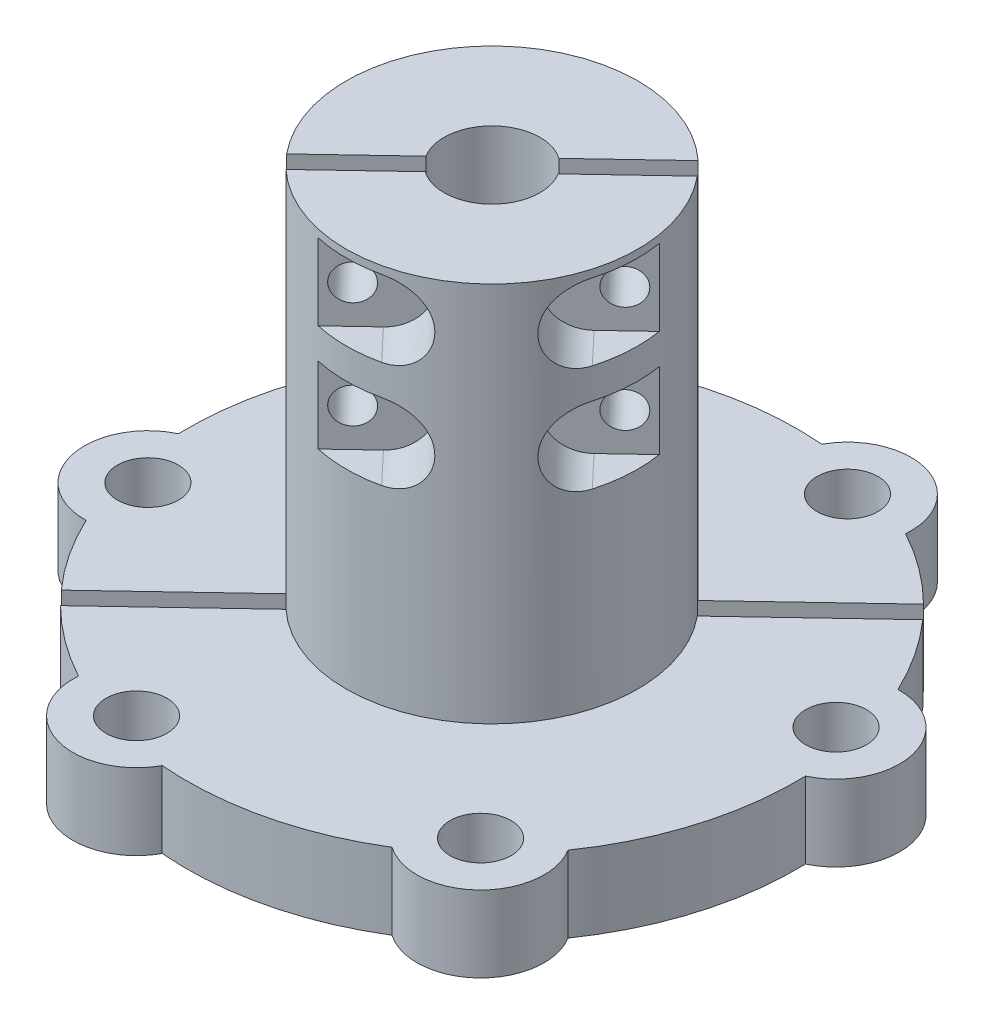
SolidWorks part; units mm, degrees
ref_plane "Front" through (0, 0, 0) normal (0, 0, 1) x (1, 0, 0)
ref_plane "Top" through (0, 0, 0) normal (0, 1, 0) x (1, 0, 0)
ref_plane "Right" through (0, 0, 0) normal (1, 0, 0) x (0, 0, -1)
sketch "Sketch1" plane through (0, 0, 0) normal (0, 1, 0) x (1, 0, 0)
  circle A0 centre (0, 0) radius 29.3688
  circle A1 centre (0, 0) radius 4
  dimension "D1" = 58.7375
  dimension "D2" = 8
extrude "Boss-Extrude1" add sketch "Sketch1" along normal blind 6.35
sketch "Sketch3" plane through (0, 6.35, 0) normal (0, 1, 0) x (1, 0, 0)
  circle A0 centre (0, 0) radius 4 construction
  circle A1 centre (0, 0) radius 4
  circle A2 centre (0, 0) radius 12.1539
  dimension "D1" = 24.3078
extrude "Boss-Extrude2" add sketch "Sketch3" along normal blind 31.75
sketch "Sketch4" plane through (0, 6.35, 0) normal (0, 1, 0) x (1, 0, 0)
  circle A0 centre (0, 0) radius 51.9218
  arc A1 (25.4208, 0.7099) -> (23.0191, 10.8093) centre (23.1665, 5.5091) ccw
  arc A2 (23.0191, 10.8093) -> (12.0949, 22.3703) centre (0, 0) ccw
  arc A3 (12.0949, 22.3703) -> (2.1481, 25.3398) centre (6.8115, 22.8166) ccw
  arc A4 (2.1481, 25.3398) -> (-13.3267, 21.6591) centre (0, 0) ccw
  arc A5 (-13.3267, 21.6591) -> (-20.8715, 14.5293) centre (-16.3548, 17.3065) ccw
  arc A6 (-20.8715, 14.5293) -> (-25.4207, -0.7121) centre (0, 0) ccw
  arc A7 (-25.4207, -0.7121) -> (-23.0182, -10.8112) centre (-23.166, -5.5111) ccw
  arc A8 (-23.0182, -10.8112) -> (-12.0943, -22.3707) centre (0, 0) ccw
  arc A9 (-12.0943, -22.3707) -> (-2.1466, -25.3399) centre (-6.811, -22.8186) ccw
  arc A10 (-2.1466, -25.3399) -> (13.3255, -21.6599) centre (0, 0) ccw
  arc A11 (13.3255, -21.6599) -> (20.8711, -14.5299) centre (16.3552, -17.3085) ccw
  arc A12 (25.6787, 0.5533) -> (23.1789, 11.0653) centre (23.1665, 5.5091) ccw
  arc A13 (21.1727, -14.5402) -> (25.6787, 0.5533) centre (0, 0) ccw
  arc A14 (13.3188, -21.9616) -> (21.1727, -14.5402) centre (16.3552, -17.3085) ccw
  arc A15 (-2.0047, -25.6063) -> (13.3188, -21.9616) centre (0, 0) ccw
  arc A16 (-12.359, -22.5157) -> (-2.0047, -25.6063) centre (-6.811, -22.8186) ccw
  arc A17 (-23.178, -11.0673) -> (-12.359, -22.5157) centre (0, 0) ccw
  arc A18 (-25.6787, -0.5554) -> (-23.178, -11.0673) centre (-23.166, -5.5111) ccw
  arc A19 (-21.1731, 14.5397) -> (-25.6787, -0.5554) centre (0, 0) ccw
  arc A20 (-13.3201, 21.9608) -> (-21.1731, 14.5397) centre (-16.3548, 17.3065) ccw
  arc A21 (2.0063, 25.6062) -> (-13.3201, 21.9608) centre (0, 0) ccw
  arc A22 (12.3596, 22.5154) -> (2.0063, 25.6062) centre (6.8115, 22.8166) ccw
  arc A23 (23.1789, 11.0653) -> (12.3596, 22.5154) centre (0, 0) ccw
  arc A24 (25.6787, 0.5533) -> (23.1789, 11.0653) centre (23.1665, 5.5091) ccw construction
  arc A25 (21.1727, -14.5402) -> (25.6787, 0.5533) centre (0, 0) ccw construction
  arc A26 (13.3188, -21.9616) -> (21.1727, -14.5402) centre (16.3552, -17.3085) ccw construction
  arc A27 (-2.0047, -25.6063) -> (13.3188, -21.9616) centre (0, 0) ccw construction
  arc A28 (-12.359, -22.5157) -> (-2.0047, -25.6063) centre (-6.811, -22.8186) ccw construction
  arc A29 (-23.178, -11.0673) -> (-12.359, -22.5157) centre (0, 0) ccw construction
  arc A30 (-25.6787, -0.5554) -> (-23.178, -11.0673) centre (-23.166, -5.5111) ccw construction
  arc A31 (-21.1731, 14.5397) -> (-25.6787, -0.5554) centre (0, 0) ccw construction
  arc A32 (-13.3201, 21.9608) -> (-21.1731, 14.5397) centre (-16.3548, 17.3065) ccw construction
  arc A33 (2.0063, 25.6062) -> (-13.3201, 21.9608) centre (0, 0) ccw construction
  arc A34 (12.3596, 22.5154) -> (2.0063, 25.6062) centre (6.8115, 22.8166) ccw construction
  arc A35 (23.1789, 11.0653) -> (12.3596, 22.5154) centre (0, 0) ccw construction
  arc A36 (20.8711, -14.5299) -> (25.4208, 0.7099) centre (0, 0) ccw
  dimension "D2" = 0.254
  dimension "D1" = 0
extrude "Cut-Extrude1" cut sketch "Sketch4" against normal through all
sketch "Sketch5" plane through (0, 6.35, 0) normal (0, 1, 0) x (1, 0, 0)
  circle A0 centre (-23.166, -5.5111) radius 2.54 construction
  circle A1 centre (-6.811, -22.8186) radius 2.54 construction
  circle A2 centre (16.3552, -17.3085) radius 2.54 construction
  circle A3 centre (23.1665, 5.5091) radius 2.54 construction
  circle A4 centre (6.8115, 22.8166) radius 2.54 construction
  circle A5 centre (-16.3548, 17.3065) radius 2.54 construction
  circle A6 centre (-23.166, -5.5111) radius 2.54
  circle A7 centre (-6.811, -22.8186) radius 2.54
  circle A8 centre (16.3552, -17.3085) radius 2.54
  circle A9 centre (23.1665, 5.5091) radius 2.54
  circle A10 centre (6.8115, 22.8166) radius 2.54
  circle A11 centre (-16.3548, 17.3065) radius 2.54
extrude "Cut-Extrude2" cut sketch "Sketch5" against normal through all
sketch "Sketch6" plane through (0, 0, 0) normal (0, -1, 0) x (1, 0, 0)
  circle A0 centre (0, 0) radius 9.525
  dimension "D1" = 19.05
extrude "Cut-Extrude3" cut sketch "Sketch6" against normal blind 12.7
sketch "Outline" plane through (0, 0, 0) normal (0, -1, 0) x (1, 0, 0)
  circle A0 centre (0, 0) radius 9.525 construction
  circle A1 centre (0, 0) radius 9.525
  arc A12 (25.4208, -0.7099) -> (20.8711, 14.5299) centre (0, 0) ccw
  arc A13 (20.8711, 14.5299) -> (13.3255, 21.6599) centre (16.3552, 17.3085) ccw
  arc A14 (13.3255, 21.6599) -> (-2.1466, 25.3399) centre (0, 0) ccw
  arc A15 (-2.1466, 25.3399) -> (-12.0943, 22.3707) centre (-6.811, 22.8186) ccw
  arc A16 (-12.0943, 22.3707) -> (-23.0182, 10.8112) centre (0, 0) ccw
  arc A17 (-23.0182, 10.8112) -> (-25.4207, 0.7121) centre (-23.166, 5.5111) ccw
  arc A18 (-25.4207, 0.7121) -> (-20.8715, -14.5293) centre (0, 0) ccw
  arc A19 (-20.8715, -14.5293) -> (-13.3267, -21.6591) centre (-16.3548, -17.3065) ccw
  arc A20 (-13.3267, -21.6591) -> (2.1481, -25.3398) centre (0, 0) ccw
  arc A21 (2.1481, -25.3398) -> (12.0949, -22.3703) centre (6.8115, -22.8166) ccw
  arc A22 (12.0949, -22.3703) -> (23.0191, -10.8093) centre (0, 0) ccw
  arc A23 (23.0191, -10.8093) -> (25.4208, -0.7099) centre (23.1665, -5.5091) ccw
  arc A24 (25.4208, -0.7099) -> (20.8711, 14.5299) centre (0, 0) ccw
  arc A25 (20.8711, 14.5299) -> (13.3255, 21.6599) centre (16.3552, 17.3085) ccw
  arc A26 (13.3255, 21.6599) -> (-2.1466, 25.3399) centre (0, 0) ccw
  arc A27 (-2.1466, 25.3399) -> (-12.0943, 22.3707) centre (-6.811, 22.8186) ccw
  arc A28 (-12.0943, 22.3707) -> (-23.0182, 10.8112) centre (0, 0) ccw
  arc A29 (-23.0182, 10.8112) -> (-25.4207, 0.7121) centre (-23.166, 5.5111) ccw
  arc A30 (-25.4207, 0.7121) -> (-20.8715, -14.5293) centre (0, 0) ccw
  arc A31 (-20.8715, -14.5293) -> (-13.3267, -21.6591) centre (-16.3548, -17.3065) ccw
  arc A32 (-13.3267, -21.6591) -> (2.1481, -25.3398) centre (0, 0) ccw
  arc A33 (2.1481, -25.3398) -> (12.0949, -22.3703) centre (6.8115, -22.8166) ccw
  arc A34 (12.0949, -22.3703) -> (23.0191, -10.8093) centre (0, 0) ccw
  arc A35 (23.0191, -10.8093) -> (25.4208, -0.7099) centre (23.1665, -5.5091) ccw
  dimension "D1" = 0
sketch "Sketch7" plane through (0, 0, 0) normal (0, -1, 0) x (1, 0, 0)
  line L0 (-18.4831, 17.4669) -> (18.4841, -17.4659) construction
  line L1 (-23.8841, 21.4785) -> (22.7947, -22.6313)
  line L2 (-22.7937, 22.6323) -> (23.885, -21.4775)
  line L3 (-17.938, 18.0438) -> (19.0293, -16.889) construction
  line L4 (-19.0283, 16.89) -> (17.9389, -18.0428) construction
  arc A0 (-12.0943, 22.3707) -> (-23.0182, 10.8112) centre (0, 0) ccw construction
  arc A1 (12.0949, -22.3703) -> (23.0191, -10.8093) centre (0, 0) ccw construction
  arc A2 (-22.7937, 22.6323) -> (-23.8841, 21.4785) centre (0, 0) ccw
  arc A3 (22.7947, -22.6313) -> (23.885, -21.4775) centre (0, 0) ccw
  dimension "D1" = 0.7937
  dimension "D2" = 0.7937
extrude "Slot" cut sketch "Sketch7" against normal through all
ref_plane "Plane1" through (-25.6223, 0, -27.1146) normal (-0.6868, 0, -0.7268) x (-0.7268, 0, 0.6868)
sketch "Sketch8" plane through (-25.6223, 0, -27.1146) normal (-0.6868, 0, -0.7268) x (-0.7268, 0, 0.6868)
  line L0 (8.0241, 38.1) -> (8.0241, 34.29) construction
  line L1 (8.0241, 34.29) -> (8.0241, 25.4) construction
  line L2 (3.9203, 12.7) -> (-3.9203, 12.7) construction
  line L3 (0, 12.7) -> (0, 58.6753) construction
  line L8 (12.1279, 38.1) -> (3.9203, 38.1)
  line L9 (3.9203, 38.1) -> (3.9203, 12.7)
  line L10 (3.9203, 12.7) -> (9.4918, 12.7)
  line L11 (9.4918, 12.7) -> (9.4918, 0)
  line L12 (9.4918, 0) -> (25.4183, 0)
  line L13 (25.4183, 0) -> (25.4183, 6.35)
  line L14 (25.4183, 6.35) -> (12.1279, 6.35)
  line L15 (12.1279, 6.35) -> (12.1279, 38.1)
  line L16 (12.1279, 38.1) -> (3.9203, 38.1) construction
  line L17 (3.9203, 38.1) -> (3.9203, 12.7) construction
  line L18 (3.9203, 12.7) -> (9.4918, 12.7) construction
  line L19 (9.4918, 12.7) -> (9.4918, 0) construction
  line L20 (9.4918, 0) -> (25.4183, 0) construction
  line L21 (25.4183, 0) -> (25.4183, 6.35) construction
  line L22 (25.4183, 6.35) -> (12.1279, 6.35) construction
  line L23 (12.1279, 6.35) -> (12.1279, 38.1) construction
  line L24 (-12.1279, 6.35) -> (-25.4183, 6.35)
  line L25 (-25.4183, 6.35) -> (-25.4183, 0)
  line L26 (-25.4183, 0) -> (-9.4918, 0)
  line L27 (-9.4918, 0) -> (-9.4918, 12.7)
  line L28 (-9.4918, 12.7) -> (-3.9203, 12.7)
  line L29 (-3.9203, 12.7) -> (-3.9203, 38.1)
  line L30 (-3.9203, 38.1) -> (-12.1279, 38.1)
  line L31 (-12.1279, 38.1) -> (-12.1279, 6.35)
  line L32 (-12.1279, 6.35) -> (-25.4183, 6.35) construction
  line L33 (-25.4183, 6.35) -> (-25.4183, 0) construction
  line L34 (-25.4183, 0) -> (-9.4918, 0) construction
  line L35 (-9.4918, 0) -> (-9.4918, 12.7) construction
  line L36 (-9.4918, 12.7) -> (-3.9203, 12.7) construction
  line L37 (-3.9203, 12.7) -> (-3.9203, 38.1) construction
  line L38 (-3.9203, 38.1) -> (-12.1279, 38.1) construction
  line L39 (-12.1279, 38.1) -> (-12.1279, 6.35) construction
  circle A0 centre (8.0241, 34.29) radius 1.4732
  circle A1 centre (8.0241, 25.4) radius 1.4732
  circle A2 centre (-8.0241, 34.29) radius 1.4732
  circle A3 centre (-8.0241, 25.4) radius 1.4732
  dimension "D4" = 2.9464
  dimension "D3" = 3.81
  dimension "D5" = 8.89
  dimension "D1" = 0
  dimension "D2" = 0
extrude "No4-40 Holes" cut sketch "Sketch8" against normal through all
sketch "Sketch9" plane through (-25.6223, 0, -27.1146) normal (-0.6868, 0, -0.7268) x (-0.7268, 0, 0.6868)
  circle A0 centre (-8.0241, 25.4) radius 1.4732 construction
  circle A1 centre (8.0241, 34.29) radius 1.4732 construction
  circle A2 centre (8.0241, 25.4) radius 1.4732 construction
  circle A3 centre (-8.0241, 25.4) radius 1.4732 construction
  circle A4 centre (8.0241, 34.29) radius 1.4732 construction
  circle A5 centre (8.0241, 25.4) radius 1.4732 construction
  circle A6 centre (-8.0241, 34.29) radius 1.4732 construction
  circle A7 centre (-8.0241, 34.29) radius 1.4732 construction
  circle A8 centre (8.0241, 25.4) radius 2.413
  circle A9 centre (8.0241, 34.29) radius 2.413
  circle A10 centre (-8.0241, 25.4) radius 2.413
  circle A11 centre (-8.0241, 34.29) radius 2.413
  dimension "D1" = 4.826
extrude "No4-40 Counterbore" cut sketch "Sketch9" against normal blind 30.48
ref_plane "Plane2" through (25.6233, 0, 27.1156) normal (0.6868, 0, 0.7268) x (0.7268, 0, -0.6868)
sketch "Sketch10" plane through (25.6233, 0, 27.1156) normal (0.6868, 0, 0.7268) x (0.7268, 0, -0.6868)
  line L0 (6.2101, 37.465) -> (22.6115, 37.465)
  line L13 (6.2101, 31.115) -> (22.6115, 31.115)
  line L14 (22.6115, 31.115) -> (22.6115, 37.465)
  line L15 (6.2101, 28.575) -> (22.6115, 28.575)
  line L16 (22.6115, 28.575) -> (22.6115, 22.225)
  line L17 (22.6115, 22.225) -> (6.2101, 22.225)
  line L18 (-8.0241, 34.29) -> (8.0432, 34.29) construction
  line L19 (0, 31.115) -> (0, 14.3016) construction
  line L20 (-22.6115, 22.225) -> (-6.2101, 22.225)
  line L21 (-22.6115, 28.575) -> (-22.6115, 22.225)
  line L22 (-6.2101, 28.575) -> (-22.6115, 28.575)
  line L23 (-22.6115, 31.115) -> (-22.6115, 37.465)
  line L24 (-6.2101, 31.115) -> (-22.6115, 31.115)
  line L25 (-6.2101, 37.465) -> (-22.6115, 37.465)
  line L26 (3.0351, 25.4) -> (22.6115, 25.4) construction
  arc A6 (6.2101, 37.465) -> (6.2101, 31.115) centre (6.2101, 34.29) ccw
  arc A7 (6.2101, 28.575) -> (6.2101, 22.225) centre (6.2101, 25.4) ccw
  circle A8 centre (-8.0241, 34.29) radius 1.4732 construction
  circle A9 centre (-8.0241, 34.29) radius 1.4732 construction
  arc A10 (-6.2101, 28.575) -> (-6.2101, 22.225) centre (-6.2101, 25.4) cw
  arc A11 (-6.2101, 37.465) -> (-6.2101, 31.115) centre (-6.2101, 34.29) cw
  circle A12 centre (8.0241, 25.4) radius 1.4732 construction
  circle A13 centre (8.0241, 25.4) radius 1.4732 construction
  dimension "D1" = 6.35
extrude "No4-40 Nut Slots" cut sketch "Sketch10" against normal blind 30.48
sketch "Sketch12" plane through (0, 38.1, 0) normal (0, 1, 0) x (1, 0, 0)
  line L0 (-2.7473, 2.9073) -> (2.7473, -2.9073) construction
  line L1 (0, 0) -> (-2.0299, -1.9182) construction
  line L2 (-19.9965, 21.1603) -> (-26.1686, 27.6915) construction
  line L3 (-19.9965, 21.1603) -> (-8.3478, 8.8336) construction
  arc A0 (2.3049, 3.2692) -> (-3.3943, -2.1164) centre (0, 0) ccw construction
  arc A1 (-2.3037, -3.27) -> (3.395, 2.1151) centre (0, 0) ccw construction
  circle A2 centre (0, 0) radius 38.1
  arc A3 (-13.3267, 21.6591) -> (-20.8715, 14.5293) centre (-16.3548, 17.3065) ccw construction
  arc A4 (-13.3267, 21.6591) -> (-20.8715, 14.5293) centre (-16.3548, 17.3065) ccw
  circle A5 centre (0, 0) radius 12.1539 construction
  arc A7 (8.2702, 8.9062) -> (-9.3596, -7.7534) centre (0, 0) ccw construction
  dimension "D1" = 76.2
sketch "Sketch13" plane through (4.6889, 0, 4.962) normal (0.6868, 0, 0.7268) x (0.7268, 0, -0.6868)
  line L0 (-8.0241, 34.29) -> (0, 34.29) construction
  line L1 (0, 38.1) -> (0, 25.4) construction
  line L2 (12.1279, 38.1) -> (-12.1279, 38.1) construction
  line L3 (12.1279, 38.1) -> (-12.1279, 38.1)
  line L4 (-8.0241, 25.4) -> (0, 25.4) construction
  arc A0 (-6.2101, 31.115) -> (-6.2101, 37.465) centre (-6.2101, 34.29) ccw construction
  arc A2 (-10.0563, 24.0989) -> (-10.0563, 26.7011) centre (-8.0241, 25.4) ccw construction
  arc A3 (-10.0563, 24.0989) -> (-10.0563, 26.7011) centre (-8.0241, 25.4) ccw
  arc A4 (-10.0563, 32.9889) -> (-10.0563, 35.5911) centre (-8.0241, 34.29) ccw construction
  arc A5 (-10.0563, 32.9889) -> (-10.0563, 35.5911) centre (-8.0241, 34.29) ccw
  dimension "D1" = 3.81
  dimension "D2" = 12.7
  dimension "D3" = 8.0241
sketch "Sketch14" plane through (0, 38.1, 0) normal (0, 1, 0) x (1, 0, 0)
  line L0 (4.6889, -4.962) -> (8.3476, -8.8337) construction
  line L4 (9.2026, -0.6967) -> (11.6893, -3.3283) construction
  line L5 (9.2026, -0.6967) -> (11.6893, -3.3283)
  line L6 (13.5038, 3.3677) -> (-4.1259, -13.2917) construction
  line L7 (13.5038, 3.3677) -> (-4.1259, -13.2917)
  arc A1 (-8.2692, -8.9072) -> (9.3605, 7.7523) centre (0, 0) ccw construction
  dimension "D1" = 5.3269
sketch "Sketch15" plane through (0, 38.1, 0) normal (0, 1, 0) x (1, 0, 0)
  line L0 (-8.7662, 1.1071) -> (-11.9971, -1.9459) construction
  line L1 (-8.7662, 1.1071) -> (-11.9971, -1.9459)
  line L2 (2.6212, 11.8679) -> (-0.6097, 8.8148) construction
  line L3 (2.6212, 11.8679) -> (-0.6097, 8.8148)
  line L4 (-8.7662, 1.1071) -> (-0.6097, 8.8148) construction
  line L5 (-4.6879, 4.961) -> (-8.3476, 8.8337) construction
  arc A0 (8.2702, 8.9062) -> (-9.3596, -7.7534) centre (0, 0) ccw construction
